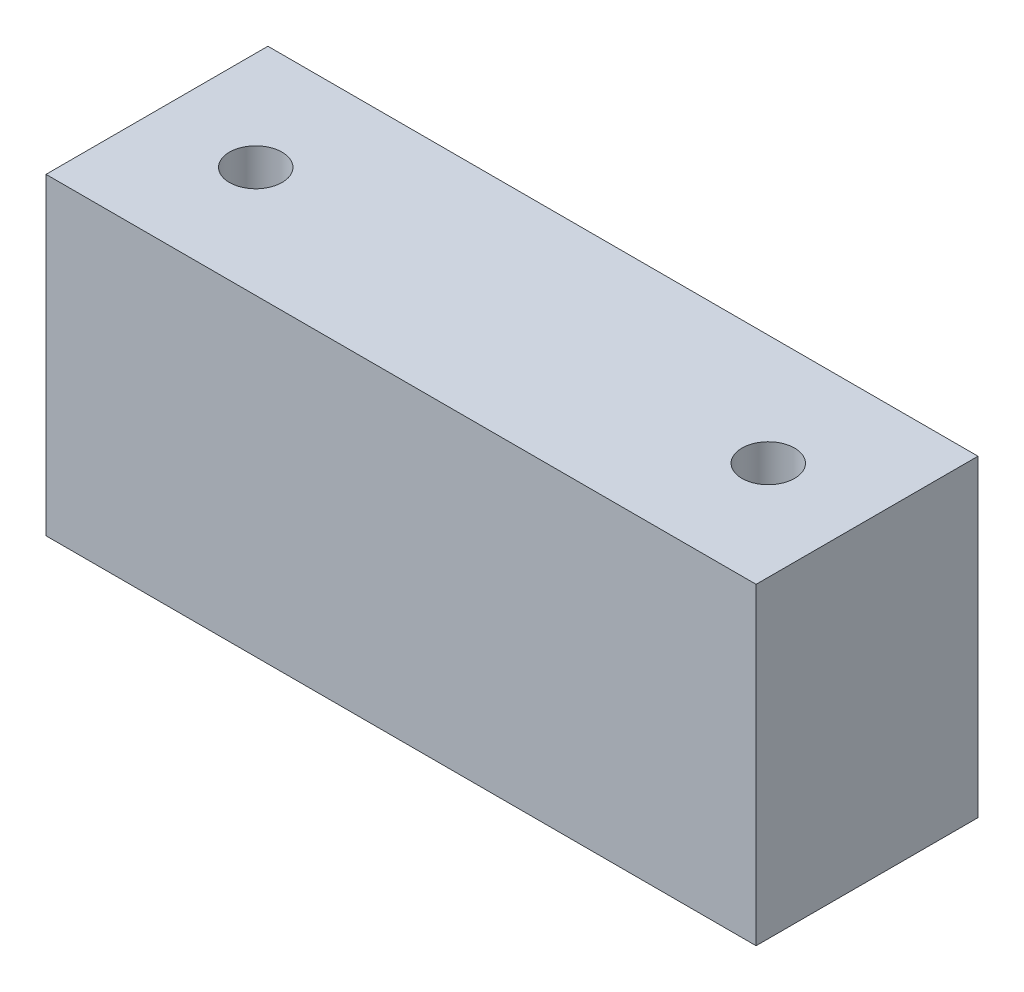
SolidWorks part; units mm, degrees
ref_plane "Front Plane" through (0, 0, 0) normal (0, 0, 1) x (1, 0, 0)
ref_plane "Top Plane" through (0, 0, 0) normal (0, 1, 0) x (1, 0, 0)
ref_plane "Right Plane" through (0, 0, 0) normal (1, 0, 0) x (0, 0, -1)
sketch "Sketch1" plane through (0, 0, 0) normal (0, 1, 0) x (1, 0, 0)
  line L1 (-15.24, -4.7625) -> (15.24, -4.7625)
  line L2 (-15.24, -4.7625) -> (-15.24, 4.7625)
  line L3 (-15.24, 4.7625) -> (15.24, 4.7625)
  line L4 (15.24, -4.7625) -> (15.24, 4.7625)
  line L5 (-15.24, -4.7625) -> (15.24, 4.7625) construction
  line L6 (-15.24, 4.7625) -> (15.24, -4.7625) construction
  point P0 (0, 0)
  dimension "D1" = 9.525
  dimension "D2" = 30.48
extrude "Boss-Extrude1" add sketch "Sketch1" along normal blind 13.4366
sketch "Sketch2" plane through (0, 13.4366, 0) normal (0, 1, 0) x (1, 0, 0)
  line L0 (-11, 0) -> (11, 0) construction
  circle A0 centre (-11, 0) radius 1.1303
  circle A1 centre (11, 0) radius 1.1303
  dimension "D2" = 2.2606
  dimension "D3" = 2.2606
  dimension "D1" = 22
extrude "Cut-Extrude1" cut sketch "Sketch2" against normal through all
